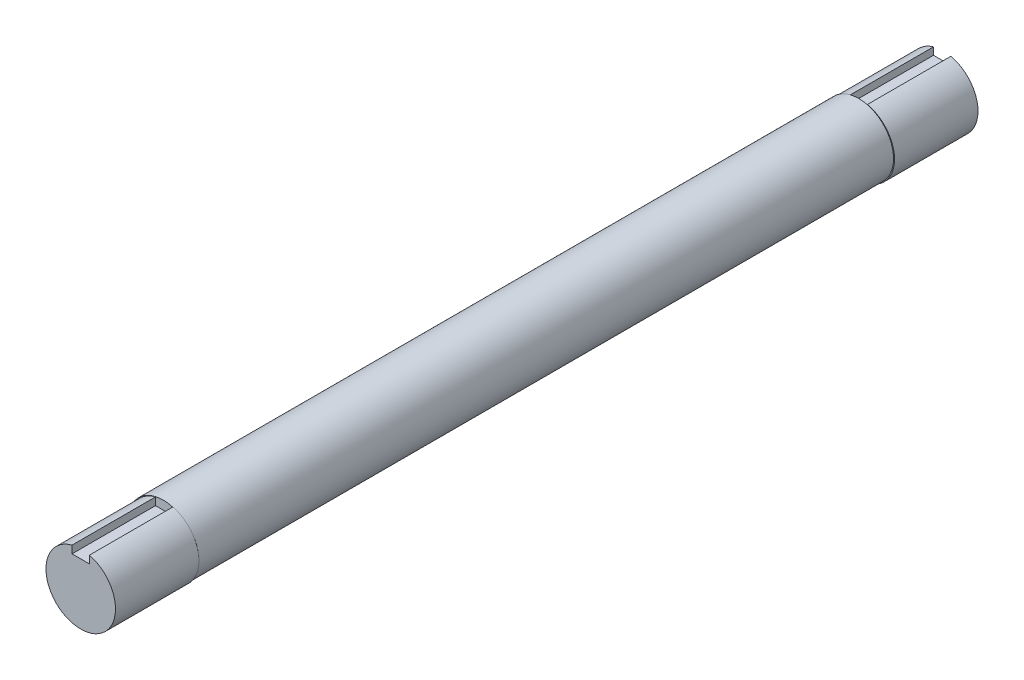
SolidWorks part; units mm, degrees
ref_plane "Front Plane" through (0, 0, 0) normal (0, 0, 1) x (1, 0, 0)
ref_plane "Top Plane" through (0, 0, 0) normal (0, 1, 0) x (1, 0, 0)
ref_plane "Right Plane" through (0, 0, 0) normal (1, 0, 0) x (0, 0, -1)
sketch "Sketch2" plane through (0, 0, 0) normal (0, 0, 1) x (1, 0, 0)
  circle A0 centre (-3.6987, 0) radius 127
extrude "Boss-Extrude1" add sketch "Sketch2" along normal blind 2540
sketch "Sketch4" plane through (0, 0, 2540) normal (0, 0, 1) x (1, 0, 0)
  line L2 (-31.75, 122.9116) -> (-31.75, 95.1961)
  line L3 (-31.75, 95.1961) -> (31.75, 95.1961)
  line L4 (31.75, 122.9116) -> (31.75, 95.1961)
  line L5 (-31.75, 158.6961) -> (31.75, 95.1961) construction
  line L6 (-31.75, 95.1961) -> (31.75, 158.6961) construction
  circle A0 centre (-3.6987, 0) radius 127 construction
  arc A1 (-31.75, 122.9116) -> (31.75, 122.9116) centre (0, 0) ccw
  point P0 (0, 126.9461)
  dimension "D1" = 63.5
extrude "Boss-Extrude2" add sketch "Sketch4" along normal blind 304.8
sketch "Sketch5" plane through (0, 0, 0) normal (0, 0, -1) x (-1, 0, 0)
  line L2 (-28.0513, 123.9186) -> (-28.0513, 95.25)
  line L3 (-28.0513, 95.25) -> (35.4487, 95.25)
  line L4 (35.4487, 122.0085) -> (35.4487, 95.25)
  line L5 (-28.0513, 158.75) -> (35.4487, 95.25) construction
  line L6 (-28.0513, 95.25) -> (35.4487, 158.75) construction
  circle A0 centre (3.6987, 0) radius 127 construction
  arc A1 (-28.0513, 123.9186) -> (35.4487, 122.0085) centre (0, 0) ccw
  point P0 (3.6987, 127)
extrude "Boss-Extrude3" add sketch "Sketch5" along normal blind 304.8
